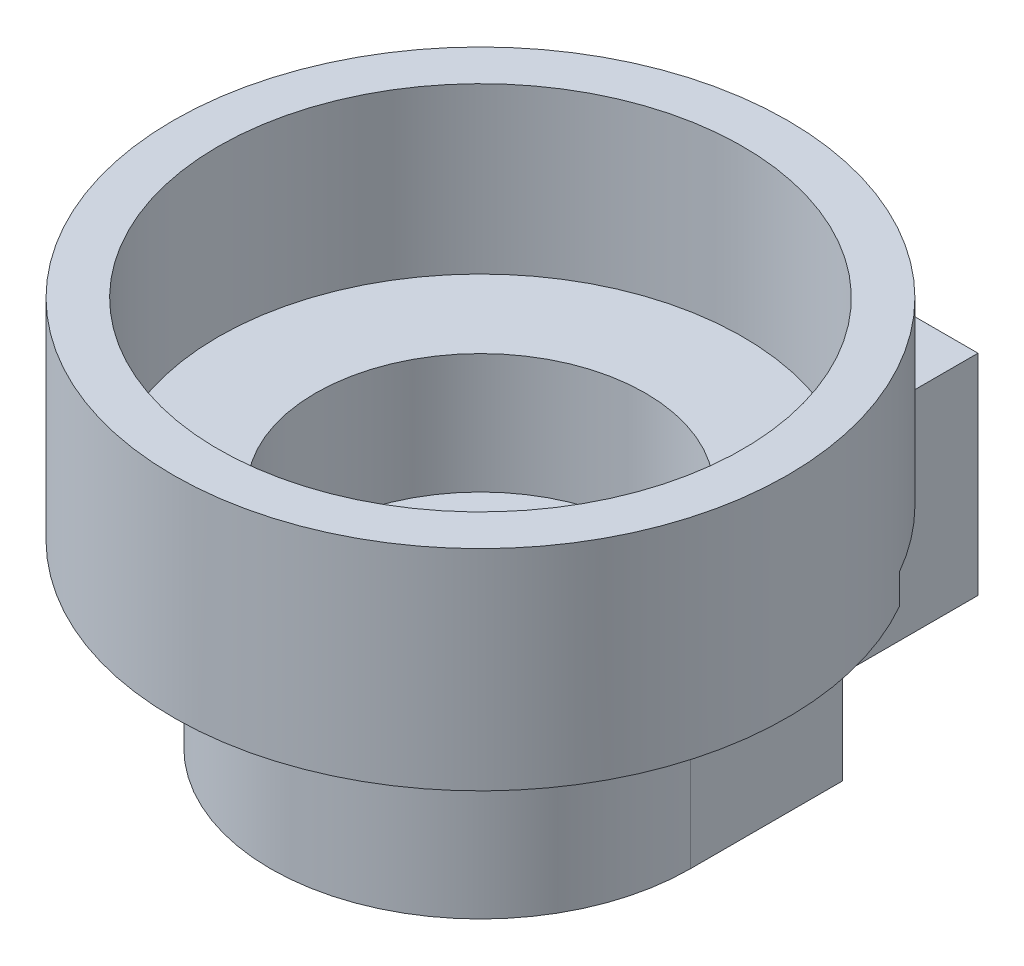
SolidWorks part; units mm, degrees
ref_plane "Front Plane" through (0, 0, 0) normal (0, 0, 1) x (1, 0, 0)
ref_plane "Top Plane" through (0, 0, 0) normal (0, 1, 0) x (1, 0, 0)
ref_plane "Right Plane" through (0, 0, 0) normal (1, 0, 0) x (0, 0, -1)
sketch "Sketch1" plane through (0, 0, 0) normal (0, 0, 1) x (1, 0, 0)
  line L0 (0, 0) -> (-14, 0)
  line L1 (-14, 0) -> (-14, 12)
  line L2 (-14, 12) -> (-20.5, 12)
  line L3 (-20.5, 12) -> (-20.5, 26)
  line L4 (-20.5, 26) -> (-17.5, 26)
  line L5 (-17.5, 26) -> (-17.5, 15)
  line L6 (-17.5, 15) -> (-11, 15)
  line L7 (-11, 15) -> (-11, 7)
  line L8 (-11, 7) -> (0, 7)
  line L9 (0, 7) -> (0, 0)
  dimension "D1" = 7
  dimension "D2" = 8
  dimension "D3" = 11
  dimension "D4" = 11
  dimension "D5" = 17.5
  dimension "D6" = 3
  dimension "D7" = 3
  dimension "D8" = 3
revolve "Revolve1" add sketch "Sketch1" angle 360 about L9
sketch "Sketch2" plane through (0, 0, 0) normal (0, -1, 0) x (1, 0, 0)
  circle A0 centre (0, 0) radius 4.15
  dimension "D1" = 8.3
extrude "Cut-Extrude1" cut sketch "Sketch2" against normal through all
sketch "Sketch3" plane through (0, 12, 0) normal (0, -1, 0) x (1, 0, 0)
  line L0 (-14, 0) -> (-14, -25.4)
  line L1 (-14, -25.4) -> (14, -25.4)
  line L2 (14, -25.4) -> (14, 0)
  circle A0 centre (0, 0) radius 14 construction
  arc A1 (-14, 0) -> (14, 0) centre (0, 0) ccw
  dimension "D1" = 25.4
extrude "Boss-Extrude1" add sketch "Sketch3" along normal up to surface (12 mm away) up to face at (0, 0, -4.15)
sketch "Sketch4" plane through (0, 0, 0) normal (0, -1, 0) x (1, 0, 0)
  circle A0 centre (0, -18.1) radius 4.625
  dimension "D1" = 9.25
  dimension "D2" = 18.1
extrude "Cut-Extrude2" cut sketch "Sketch4" against normal blind 10.62
sketch "Sketch5" plane through (-14, 0, 0) normal (-1, 0, 0) x (0, 0, 1)
  line L0 (0, 0) -> (-25.4, 0) construction
  circle A0 centre (-18.1, 6) radius 2
  dimension "D2" = 4
  dimension "D1" = 6
  dimension "D3" = 18.1
extrude "Cut-Extrude3" cut sketch "Sketch5" against normal blind 22.86
sketch "Sketch6" plane through (0, 12, 0) normal (0, 1, 0) x (1, 0, 0)
  line L3 (14, 14.975) -> (14, 25.4)
  line L4 (14, 25.4) -> (-14, 25.4)
  line L5 (-14, 25.4) -> (-14, 14.975)
  line L6 (14, 14.975) -> (14, 25.4)
  line L7 (14, 25.4) -> (-14, 25.4)
  line L8 (-14, 25.4) -> (-14, 14.975)
  arc A1 (14, 14.975) -> (-14, 14.975) centre (0, 0) ccw
  arc A2 (14, 14.975) -> (-14, 14.975) centre (0, 0) ccw
  dimension "D1" = 0
extrude "Boss-Extrude2" add sketch "Sketch6" along normal blind 2
ref_plane "Plane1" through (-20.5, 0, 0) normal (-1, 0, 0) x (0, 0, 1)
sketch "Sketch7" plane through (-20.5, 0, 0) normal (-1, 0, 0) x (0, 0, 1)
  line L1 (0, 0) -> (-25.4, 0) construction
  line L2 (-10.16, 0) -> (-10.16, 14)
  line L6 (-25.4, 0) -> (0, 0)
  line L7 (0, 0) -> (0, 12)
  line L8 (0, 12) -> (-14.975, 12)
  line L9 (-14.975, 12) -> (-14.975, 14)
  line L10 (-14.975, 14) -> (-25.4, 14)
  line L11 (-25.4, 14) -> (-25.4, 0)
  line L12 (-25.4, 0) -> (-10.16, 0)
  line L16 (-10.16, 14) -> (-25.4, 14)
  line L17 (-25.4, 14) -> (-25.4, 0)
  dimension "D2" = 15.24
  dimension "D1" = 0
extrude "Cut-Extrude4" cut sketch "Sketch7" against normal blind 12.7
mirror "Mirror1" about plane through (0, 0, 0) normal (1, 0, 0) of "Cut-Extrude4"
